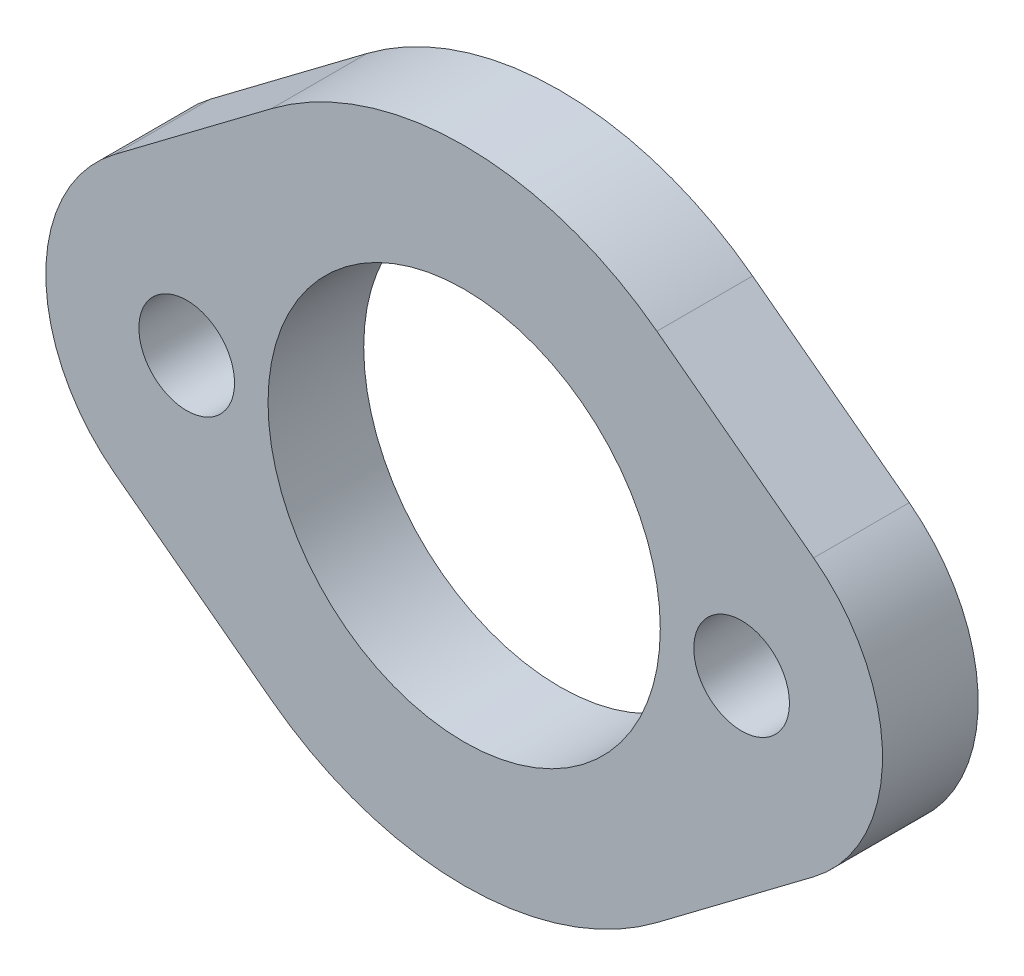
SolidWorks part; units mm, degrees
ref_plane "Front Plane" through (0, 0, 0) normal (0, 0, 1) x (1, 0, 0)
ref_plane "Top Plane" through (0, 0, 0) normal (0, 1, 0) x (1, 0, 0)
ref_plane "Right Plane" through (0, 0, 0) normal (1, 0, 0) x (0, 0, -1)
sketch "Sketch1" plane through (0, 0, 0) normal (0, 0, 1) x (1, 0, 0)
  line L0 (41.088, 0) -> (-41.088, 0) construction
  line L1 (0, 43.3083) -> (0, -22.4248) construction
  line L12 (-18.2629, -7.2177) -> (-10.0735, -13.3823)
  line L13 (10.0735, -13.3823) -> (18.2629, -7.2177)
  line L14 (18.2629, 7.2177) -> (10.0735, 13.3823)
  line L15 (-10.0735, 13.3823) -> (-18.2629, 7.2177)
  circle A7 centre (14.5, 0) radius 2.5
  arc A12 (-18.2629, 7.2177) -> (-18.2629, -7.2177) centre (-12.8298, 0) ccw
  arc A13 (-10.0735, -13.3823) -> (10.0735, -13.3823) centre (0, 0) ccw
  arc A14 (18.2629, -7.2177) -> (18.2629, 7.2177) centre (12.8298, 0) ccw
  arc A15 (10.0735, 13.3823) -> (-10.0735, 13.3823) centre (0, 0) ccw
  circle A16 centre (-14.5, 0) radius 2.5
  circle A17 centre (0, 0) radius 10.25
  point P3 (0, 0)
  point P6 (0, 0)
  dimension "D1" = 20.5
  dimension "D2" = 5
  dimension "D3" = 16.75
  dimension "D4" = 9.0341
  dimension "D5" = 10.0735
  dimension "D6" = 29
extrude "Boss-Extrude1" add sketch "Sketch1" along normal blind 5
